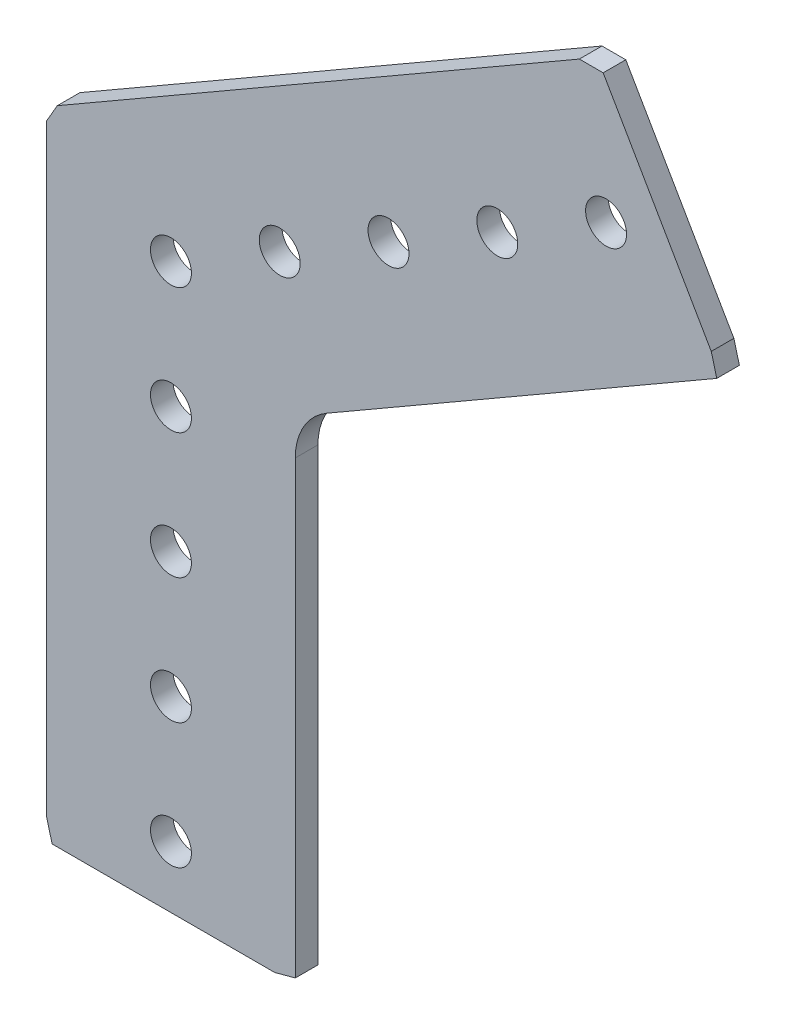
SolidWorks part; units mm, degrees
ref_plane "Front Plane" through (0, 0, 0) normal (0, 0, 1) x (1, 0, 0)
ref_plane "Top Plane" through (0, 0, 0) normal (0, 1, 0) x (1, 0, 0)
ref_plane "Right Plane" through (0, 0, 0) normal (1, 0, 0) x (0, 0, -1)
ref_plane "Plane1" through (0, 0, 2.286) normal (0, 0, 1) x (1, 0, 0)
sketch "Sketch1" plane through (0, 0, 2.286) normal (0, 0, 1) x (1, 0, 0)
  line L0 (41.2908, 38.3573) -> (-11.4935, 7.8823)
  line L1 (-11.4935, 7.8823) -> (-12.573, 6.0125)
  line L2 (-12.573, 6.0125) -> (-12.573, -54.9376)
  line L3 (-12.573, -54.9376) -> (-12.0142, -57.023)
  line L4 (-12.0142, -57.023) -> (10.4876, -57.023)
  line L5 (10.4876, -57.023) -> (12.573, -56.4642)
  line L6 (12.573, -56.4642) -> (12.573, -10.9252)
  line L7 (15.748, -5.4259) -> (55.1859, 17.3436)
  line L8 (55.1859, 17.3436) -> (54.6271, 19.429)
  line L9 (54.6271, 19.429) -> (43.6989, 38.3573)
  line L10 (43.6989, 38.3573) -> (41.2908, 38.3573)
  arc A0 (12.573, -10.9252) -> (15.748, -5.4259) centre (18.923, -10.9252) cw
  circle A1 centre (0, 0) radius 2.0701
  circle A2 centre (0, -38.1) radius 2.0701
  circle A3 centre (0, -12.7) radius 2.0701
  circle A4 centre (0, -25.4) radius 2.0701
  circle A5 centre (0, -50.8) radius 2.0701
  circle A6 centre (32.9956, 19.05) radius 2.0701
  circle A7 centre (10.9985, 6.35) radius 2.0701
  circle A8 centre (21.997, 12.7) radius 2.0701
  circle A9 centre (43.9941, 25.4) radius 2.0701
extrude "Boss-Extrude1" add sketch "Sketch1" against normal blind 2.286
